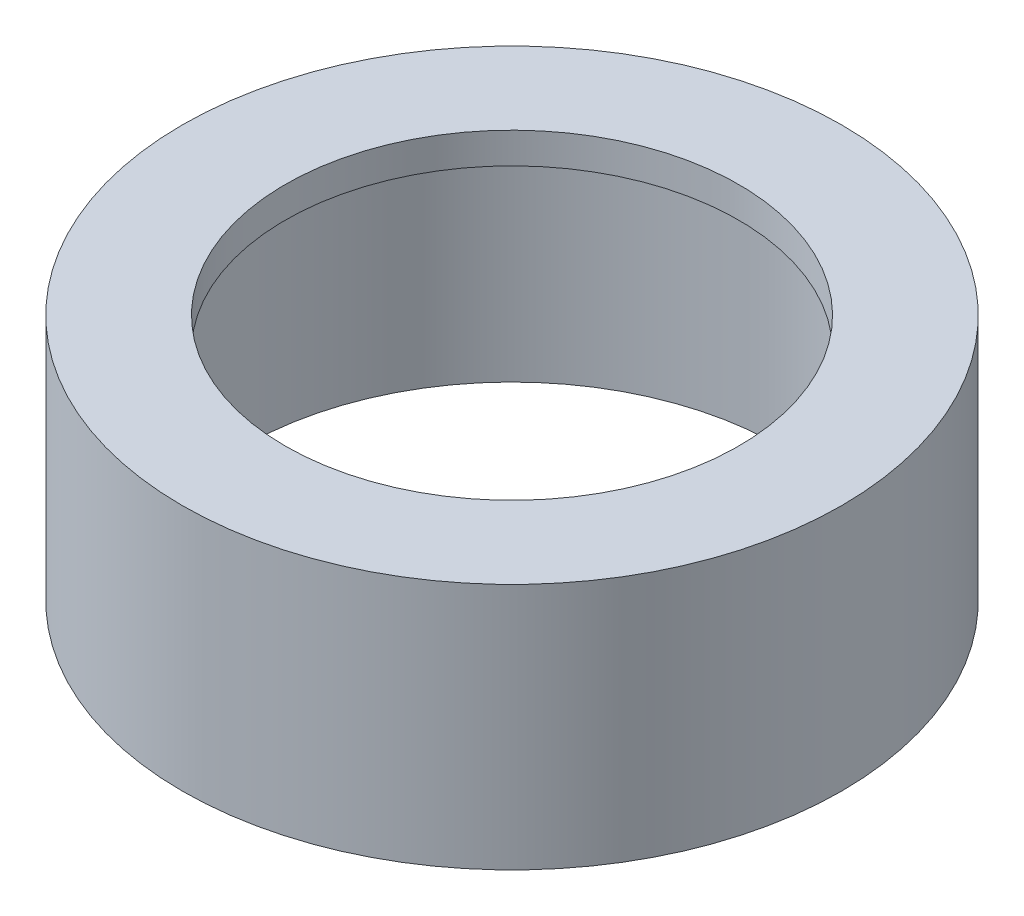
SolidWorks part; units mm, degrees
material "1060 Alloy"
ref_plane "Front Plane" through (0, 0, 0) normal (0, 0, 1) x (1, 0, 0)
ref_plane "Top Plane" through (0, 0, 0) normal (0, 1, 0) x (1, 0, 0)
ref_plane "Right Plane" through (0, 0, 0) normal (1, 0, 0) x (0, 0, -1)
sketch "Sketch1" plane through (0, 0, 0) normal (0, 1, 0) x (1, 0, 0)
  circle A0 centre (0, 0) radius 16
  circle A1 centre (0, 0) radius 13
  dimension "D1" = 32
  dimension "D2" = 26
extrude "Boss-Extrude1" add sketch "Sketch1" along normal blind 12
sketch "Sketch2" plane through (0, 12, 0) normal (0, 1, 0) x (1, 0, 0)
  circle A0 centre (0, 0) radius 13
  circle A1 centre (0, 0) radius 11
extrude "Boss-Extrude2" add sketch "Sketch2" against normal blind 1.5
